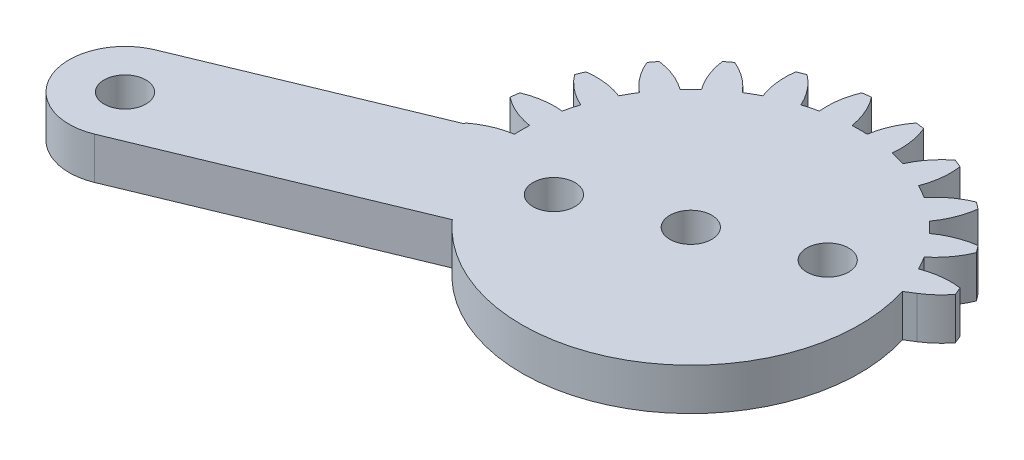
SolidWorks part; units mm, degrees
ref_plane "Front" through (0, 0, 0) normal (0, 0, 1) x (1, 0, 0)
ref_plane "Top" through (0, 0, 0) normal (0, 1, 0) x (1, 0, 0)
ref_plane "Right" through (0, 0, 0) normal (1, 0, 0) x (0, 0, -1)
sketch "Sketch1" plane through (0, 0, 0) normal (0, 1, 0) x (1, 0, 0)
  line L0 (-9.0649, -8.1356) -> (-27.1619, -15.6316)
  line L1 (-14.5796, -1.7607) -> (-30.2233, -8.2406)
  line L2 (12.1357, 3.9271) -> (11.4921, 3.5272)
  arc A0 (-30.2233, -8.2406) -> (-27.1619, -15.6316) centre (-28.6926, -11.9361) ccw
  arc A1 (-14.5896, -1.672) -> (-14.5796, -1.7607) centre (-0.0523, -0.0729) ccw
  arc A2 (-12.1329, -0.6156) -> (-14.5896, -1.672) centre (-11.2946, -5.9502) ccw
  arc A3 (-12.1329, 0.4698) -> (-12.1329, -0.6156) centre (-0.0523, -0.0729) ccw
  arc A4 (-14.5896, 1.5262) -> (-12.1329, 0.4698) centre (-11.2946, 5.8044) ccw
  arc A5 (-14.5082, 2.145) -> (-14.5896, 1.5262) centre (-0.0523, -0.0729) ccw
  arc A6 (-11.8617, 2.5296) -> (-14.5082, 2.145) centre (-12.4327, -2.8402) ccw
  arc A7 (-11.5808, 3.578) -> (-11.8617, 2.5296) centre (-0.0523, -0.0729) ccw
  arc A8 (-13.6804, 5.2342) -> (-11.5808, 3.578) centre (-9.3904, 8.5138) ccw
  arc A9 (-13.4416, 5.8109) -> (-13.6804, 5.2342) centre (-0.0523, -0.0729) ccw
  arc A10 (-10.7858, 5.4974) -> (-13.4416, 5.8109) centre (-12.727, 0.4584) ccw
  arc A11 (-10.243, 6.4374) -> (-10.7858, 5.4974) centre (-0.0523, -0.0729) ccw
  arc A12 (-11.8425, 8.5806) -> (-10.243, 6.4374) centre (-6.8498, 10.6381) ccw
  arc A13 (-11.4625, 9.0758) -> (-11.8425, 8.5806) centre (-0.0523, -0.0729) ccw
  arc A14 (-8.9783, 8.0856) -> (-11.4625, 9.0758) centre (-12.1577, 3.7207) ccw
  arc A15 (-8.2108, 8.8531) -> (-8.9783, 8.0856) centre (-0.0523, -0.0729) ccw
  arc A16 (-9.201, 11.3373) -> (-8.2108, 8.8531) centre (-3.846, 12.0324) ccw
  arc A17 (-8.7058, 11.7172) -> (-9.201, 11.3373) centre (-0.0523, -0.0729) ccw
  arc A18 (-6.5626, 10.1178) -> (-8.7058, 11.7172) centre (-10.7633, 6.7246) ccw
  arc A19 (-5.6226, 10.6605) -> (-6.5626, 10.1178) centre (-0.0523, -0.0729) ccw
  arc A20 (-5.9361, 13.3163) -> (-5.6226, 10.6605) centre (-0.5836, 12.6018) ccw
  arc A21 (-5.3595, 13.5552) -> (-5.9361, 13.3163) centre (-0.0523, -0.0729) ccw
  arc A22 (-3.7032, 11.4556) -> (-5.3595, 13.5552) centre (-8.639, 9.2652) ccw
  arc A23 (-2.6548, 11.7365) -> (-3.7032, 11.4556) centre (-0.0523, -0.0729) ccw
  arc A24 (-2.2703, 14.3829) -> (-2.6548, 11.7365) centre (2.715, 12.3075) ccw
  arc A25 (-1.6514, 14.4644) -> (-2.2703, 14.3829) centre (-0.0523, -0.0729) ccw
  arc A26 (-0.595, 12.0077) -> (-1.6514, 14.4644) centre (-5.9296, 11.1694) ccw
  arc A27 (0.4904, 12.0077) -> (-0.595, 12.0077) centre (-0.0523, -0.0729) ccw
  arc A28 (1.5468, 14.4644) -> (0.4904, 12.0077) centre (5.8249, 11.1694) ccw
  arc A29 (2.1656, 14.3829) -> (1.5468, 14.4644) centre (-0.0523, -0.0729) ccw
  arc A30 (2.5501, 11.7365) -> (2.1656, 14.3829) centre (-2.8196, 12.3075) ccw
  arc A31 (3.5986, 11.4556) -> (2.5501, 11.7365) centre (-0.0523, -0.0729) ccw
  arc A32 (5.2548, 13.5552) -> (3.5986, 11.4556) centre (8.5344, 9.2652) ccw
  arc A33 (5.8315, 13.3163) -> (5.2548, 13.5552) centre (-0.0523, -0.0729) ccw
  arc A34 (5.5179, 10.6605) -> (5.8315, 13.3163) centre (0.479, 12.6018) ccw
  arc A35 (6.458, 10.1178) -> (5.5179, 10.6605) centre (-0.0523, -0.0729) ccw
  arc A36 (8.6012, 11.7172) -> (6.458, 10.1178) centre (10.6587, 6.7246) ccw
  arc A37 (9.0964, 11.3373) -> (8.6012, 11.7172) centre (-0.0523, -0.0729) ccw
  arc A38 (8.1062, 8.8531) -> (9.0964, 11.3373) centre (3.7413, 12.0324) ccw
  arc A39 (8.8737, 8.0856) -> (8.1062, 8.8531) centre (-0.0523, -0.0729) ccw
  arc A40 (11.3578, 9.0758) -> (8.8737, 8.0856) centre (12.053, 3.7207) ccw
  arc A41 (11.7378, 8.5806) -> (11.3578, 9.0758) centre (-0.0523, -0.0729) ccw
  arc A42 (10.1384, 6.4374) -> (11.7378, 8.5806) centre (6.7451, 10.6381) ccw
  arc A43 (10.6811, 5.4974) -> (10.1384, 6.4374) centre (-0.0523, -0.0729) ccw
  arc A44 (13.3369, 5.8109) -> (10.6811, 5.4974) centre (12.6224, 0.4584) ccw
  arc A45 (13.5758, 5.2342) -> (13.3369, 5.8109) centre (-0.0523, -0.0729) ccw
  arc A46 (12.1357, 3.9271) -> (13.5758, 5.2342) centre (9.2857, 8.5138) ccw
  arc A47 (-9.0649, -8.1356) -> (11.4921, 3.5272) centre (-0.0523, -0.0729) ccw
  circle A48 centre (-0.0523, -0.0729) radius 1.5
  circle A49 centre (-28.6926, -11.9361) radius 1.5
  circle A50 centre (-6.9814, -2.943) radius 1.5
  circle A51 centre (6.8768, 2.7972) radius 1.5
  dimension "D1" = 3
extrude "Boss-Extrude1" add sketch "Sketch1" along normal mid plane 3
